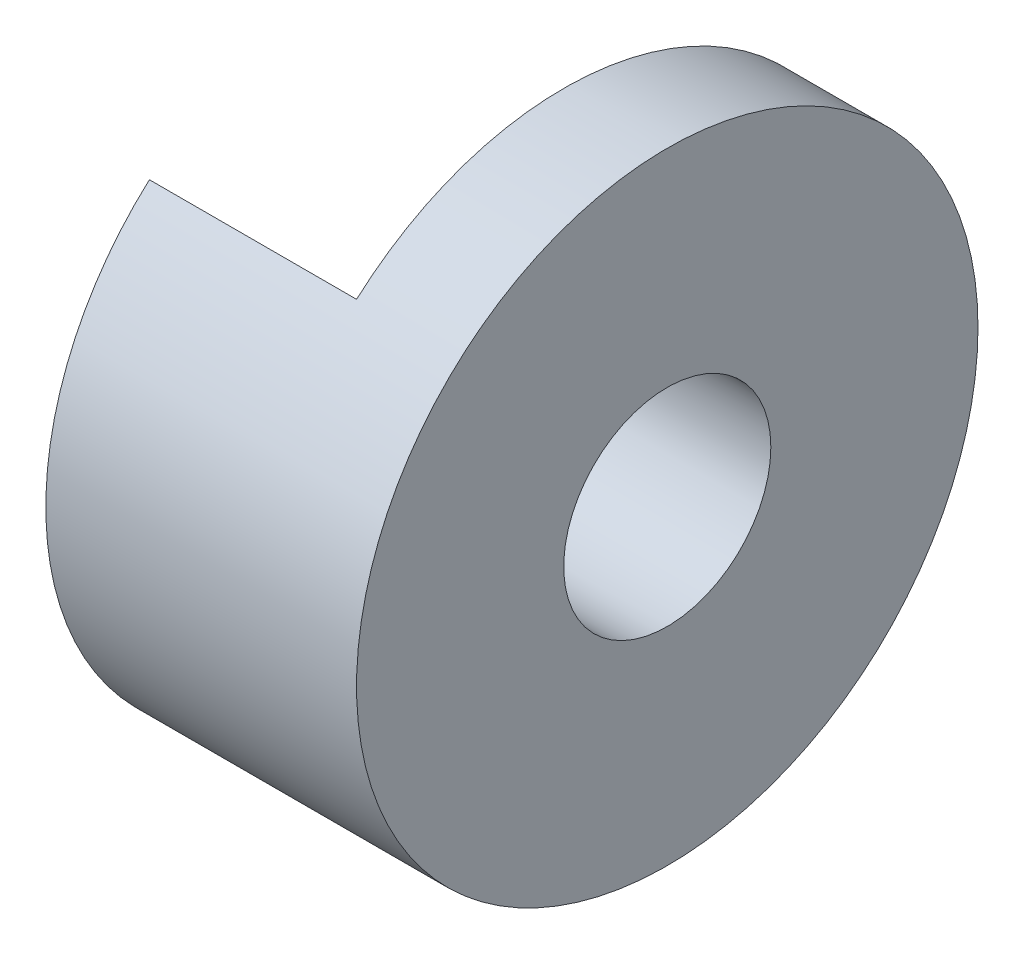
SolidWorks part; units mm, degrees
ref_plane "Front" through (0, 0, 0) normal (0, 0, 1) x (1, 0, 0)
ref_plane "Top" through (0, 0, 0) normal (0, 1, 0) x (1, 0, 0)
ref_plane "Right" through (0, 0, 0) normal (1, 0, 0) x (0, 0, -1)
sketch "Sketch1" plane through (0, 0, 0) normal (1, 0, 0) x (0, 0, -1)
  circle A0 centre (0, 0) radius 3
  circle A1 centre (0, 0) radius 1
  dimension "D1" = 2
  dimension "D2" = 6
extrude "Boss-Extrude1" add sketch "Sketch1" along normal mid plane 3
sketch "Sketch2" plane through (-1.5, 0, 0) normal (-1, 0, 0) x (0, 0, 1)
  line L0 (2, 2.2361) -> (2, -2.2361)
  line L1 (0, -1) -> (0, -3)
  line L2 (-1, 0) -> (-3, 0)
  circle A0 centre (0, 0) radius 3 construction
  circle A1 centre (0, 0) radius 1 construction
  arc A2 (-3, 0) -> (0, -3) centre (0, 0) ccw
  arc A3 (2, -2.2361) -> (2, 2.2361) centre (0, 0) ccw
  circle M2 centre (0, 0) radius 3
  circle M3 centre (0, 0) radius 1
  dimension "D1" = 2
extrude "Cut-Extrude1" cut sketch "Sketch2" against normal blind 2 contours L2 L1 L0 M3 M2
